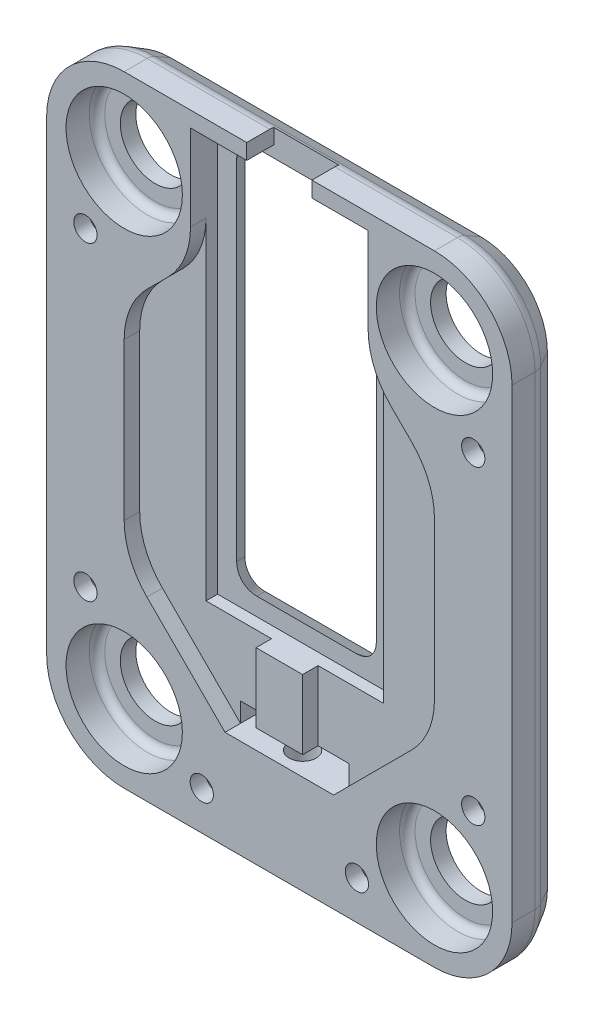
SolidWorks part; units mm, degrees
ref_plane "Front Plane" through (0, 0, 0) normal (0, 0, 1) x (1, 0, 0)
ref_plane "Top Plane" through (0, 0, 0) normal (0, 1, 0) x (1, 0, 0)
ref_plane "Right Plane" through (0, 0, 0) normal (1, 0, 0) x (0, 0, -1)
sketch "Sketch1" plane through (0, 0, 0) normal (0, 0, 1) x (1, 0, 0)
  line L1 (-11.25, 0) -> (11.25, 0) construction
  line L2 (-11.25, 0) -> (-11.25, -53) construction
  line L3 (-11.25, -53) -> (11.25, -53) construction
  line L4 (11.25, 0) -> (11.25, -53) construction
  line L5 (-4, 2) -> (4, 2) construction
  line L6 (-4, 2) -> (-4, 0) construction
  line L8 (4, 2) -> (4, 0) construction
  point P4 (0, 0)
  point P12 (0, 2)
  dimension "D1" = 22.5
  dimension "D2" = 53
  dimension "D3" = 8
  dimension "D4" = 2
sketch "Sketch2" plane through (0, 0, 0) normal (0, 0, 1) x (1, 0, 0)
  line L0 (-4, 2) -> (4, 2) construction
  line L1 (-20, 2) -> (20, 2)
  line L2 (-30, -8) -> (-30, -68)
  line L3 (-20, -78) -> (20, -78)
  line L4 (30, -8) -> (30, -68)
  arc A0 (-30, -68) -> (-20, -78) centre (-20, -68) ccw
  arc A1 (20, -78) -> (30, -68) centre (20, -68) ccw
  arc A2 (20, 2) -> (30, -8) centre (20, -8) cw
  arc A3 (-20, 2) -> (-30, -8) centre (-20, -8) ccw
  point P6 (0, 2)
  point P10 (-30, -78)
  point P15 (30, 2)
  point P18 (-30, 2)
  dimension "D3" = 10
  dimension "D1" = 60
  dimension "D2" = 80
extrude "Boss-Extrude1" add sketch "Sketch2" along normal blind 6
chamfer "Chamfer1" distance 2.5 angle 30 8 edges at (0, -78, 0) (27.0711, -75.0711, 0) (-27.0711, -75.0711, 0) (30, -38, 0) (-30, -38, 0) (27.0711, -0.9289, 0) (-27.0711, -0.9289, 0) (0, 2, 0)
fillet "Fillet1" radius 2 8 edges at (30, -38, 2.5) (27.0711, -75.0711, 2.5) (0, -78, 2.5) (-27.0711, -75.0711, 2.5) (-30, -38, 2.5) (-27.0711, -0.9289, 2.5) (0, 2, 2.5) (27.0711, -0.9289, 2.5)
sketch "Sketch10" plane through (0, 0, 6) normal (0, 0, 1) x (1, 0, 0)
  line L0 (-20, -8) -> (20, -8) construction
  line L1 (20, 2) -> (-20, 2) construction
  circle A0 centre (-20, -8) radius 4.5
  circle A1 centre (20, -8) radius 4.5
  circle A2 centre (20, -68) radius 4.5
  circle A3 centre (-20, -68) radius 4.5
  point P8 (0, -8)
  dimension "D1" = 9
  dimension "D2" = 40
  dimension "D3" = 60
  dimension "D4" = 10
extrude "Cut-Extrude1" cut sketch "Sketch10" against normal blind 6
sketch "Sketch11" plane through (0, 0, 6) normal (0, 0, 1) x (1, 0, 0)
  circle A0 centre (-20, -8) radius 7.5
  circle A1 centre (-20, -8) radius 4.5 construction
  circle A2 centre (20, -8) radius 7.5
  circle A3 centre (20, -68) radius 7.5
  circle A4 centre (-20, -68) radius 7.5
  circle A5 centre (-20, -68) radius 4.5 construction
  dimension "D1" = 15
extrude "Cut-Extrude2" cut sketch "Sketch11" against normal blind 4
sketch "Sketch12" plane through (0, 0, 6) normal (0, 0, 1) x (1, 0, 0)
  line L0 (-4.2, 2) -> (-4.2, 0)
  line L1 (-4.2, 0) -> (-11.45, 0)
  line L2 (-11.45, 0) -> (-11.45, -53.8)
  line L3 (-11.45, -53.8) -> (11.45, -53.8)
  line L4 (11.45, -53.8) -> (11.45, 0)
  line L5 (11.45, 0) -> (4.2, 0)
  line L6 (4.2, 0) -> (4.2, 2)
  line L7 (4.2, 2) -> (-4.2, 2)
  line L8 (-11.25, 0) -> (11.25, 0) construction
  line L9 (-4, 2) -> (-4, 0) construction
  line L10 (4, 2) -> (4, 0) construction
  line L11 (-11.25, 0) -> (-11.25, -53) construction
  line L12 (11.25, 0) -> (11.25, -53) construction
  line L13 (-11.25, -53) -> (11.25, -53) construction
  dimension "D1" = 0.2
  dimension "D2" = 0.2
  dimension "D3" = 0.2
  dimension "D4" = 0.2
  dimension "D5" = 0.8
  dimension "D6" = 2
extrude "Cut-Extrude3" cut sketch "Sketch12" against normal blind 3.5
sketch "Sketch13" plane through (0, 0, 2.5) normal (0, 0, 1) x (1, 0, 0)
  line L6 (-11.25, 0) -> (11.25, 0) construction
  line L7 (-9, -1.5) -> (9, -1.5)
  line L8 (-9, -1.5) -> (-9, -51.5)
  line L9 (-9, -51.5) -> (9, -51.5)
  line L10 (9, -1.5) -> (9, -51.5)
  point P6 (0, -1.5)
  dimension "D1" = 18
  dimension "D2" = 50
  dimension "D3" = 1.5
extrude "Cut-Extrude4" cut sketch "Sketch13" against normal through all draft 30
fillet "Fillet2" radius 3 4 edges at (-9.7217, -52.2217, 1.25) (9.7217, -52.2217, 1.25) (9.7217, -0.7783, 1.25) (-9.7217, -0.7783, 1.25)
hole_wizard "CBORE for M5 Hex Socket Head Cap Screw2" positions "Sketch22" profile "Sketch23" counterbore size "M5" standard "DIN" end condition through all
sketch "Sketch22" plane through (0, 0, 0) normal (0, 0, -1) x (-1, 0, 0)
  line L0 (4.2, 2) -> (20, 2) construction
  line L1 (20, -78) -> (-20, -78) construction
  line L2 (30, -8) -> (30, -68) construction
  line L3 (0, 16.14) -> (0, -89.9749) construction
  point P0 (-25, -18)
  point P2 (25, -18)
  point P4 (-10, -73)
  point P6 (10, -73)
  point P22 (25, -58)
  point P24 (-25, -58)
  dimension "D1" = 20
  dimension "D2" = 5
  dimension "D3" = 20
  dimension "D4" = 20
  dimension "D5" = 5
sketch "Sketch23" plane through (25, -18, 0) normal (1, 0, 0) x (0, 1, 0)
  line L0 (0, 0) -> (0, 6)
  line L1 (0, 6) -> (1.5, 6)
  line L3 (1.5, 6) -> (1.5, 4)
  line L4 (1.5, 4) -> (2, 4)
  line L5 (2, 4) -> (2, 0)
  line L7 (2, 0) -> (0, 0)
  line L11 (0, -6.35) -> (0, 107.95) construction
  dimension "Thru Hole Dia." = 3
  dimension "Thru Hole Depth" = 6
  dimension "C'Bore Dia." = 4
  dimension "C'Bore Depth" = 4
chamfer "Chamfer2" distance 2.5 angle 10 4 edges at (8, -73, 0) (-12, -73, 0) (-27, -18, 0) (23, -18, 0)
fillet "Fillet3" radius 1 4 edges at (-12.5, -8, 2) (-12.5, -68, 2) (27.5, -68, 2) (27.5, -8, 2)
sketch "Sketch24" plane through (0, 0, 6) normal (0, 0, 1) x (1, 0, 0)
  line L0 (-20, -78) -> (20, -78) construction
  line L1 (-7, -62.75) -> (7, -62.75)
  line L2 (-7, -62.75) -> (-7, -65.25)
  line L3 (-7, -65.25) -> (7, -65.25)
  line L4 (7, -62.75) -> (7, -65.25)
  point P6 (0, -65.25)
  dimension "D1" = 14
  dimension "D2" = 2.5
  dimension "D3" = 12.75
extrude "Cut-Extrude5" cut sketch "Sketch24" against normal through all
hole_wizard "M4 Tapped Hole1" positions "Sketch25" profile "Sketch26" tap size "M4" standard "DIN"
sketch "Sketch25" plane through (0, -78, 0) normal (0, -1, 0) x (-1, 0, 0)
  line L0 (20, -6) -> (-20, -6) construction
  point P0 (0, -3)
  dimension "D1" = 3
sketch "Sketch26" plane through (0, -78, 3) normal (1, 0, 0) x (0, 0, -1)
  line L0 (0, 0) -> (0, 12.75)
  line L1 (0, 12.75) -> (1.75, 12.75)
  line L2 (1.75, 12.75) -> (1.75, 0)
  line L5 (1.75, 0) -> (0, 0)
  line L11 (0, -6.35) -> (0, 107.95) construction
  dimension "Thread Major Dia." = 3.5
  dimension "Thru Tap Drill Depth" = 12.75
sketch "Sketch27" plane through (0, 0, 6) normal (0, 0, 1) x (1, 0, 0)
  line L0 (3, -10.75) -> (7, -10.75)
  line L1 (7, -10.75) -> (20, -23.75)
  line L2 (20, -23.75) -> (20, -52.25)
  line L3 (20, -52.25) -> (7, -65.25)
  line L4 (7, -65.25) -> (7, -64.2906)
  line L5 (7, -65.25) -> (7, -62.75) construction
  line L6 (7, -64.2906) -> (3, -64.2906)
  line L7 (3, -64.2906) -> (3, -10.75)
  line L9 (30, -68) -> (30, -8) construction
  line L10 (-20, -78) -> (20, -78) construction
  line L11 (20, 2) -> (4.2, 2) construction
  line L12 (0, 10.9936) -> (0, -34.5429) construction
  line L13 (-3, -64.2906) -> (-3, -10.75)
  line L14 (-7, -64.2906) -> (-3, -64.2906)
  line L15 (-7, -65.25) -> (-7, -64.2906)
  line L16 (-20, -52.25) -> (-7, -65.25)
  line L17 (-20, -23.75) -> (-20, -52.25)
  line L18 (-7, -10.75) -> (-20, -23.75)
  line L19 (-3, -10.75) -> (-7, -10.75)
  point P16 (12.1, 2)
  dimension "D1" = 135
  dimension "D2" = 135
  dimension "D3" = 10
  dimension "D4" = 4
  dimension "D5" = 12.75
  dimension "D7" = 12.75
extrude "Cut-Extrude6" cut sketch "Sketch27" against normal blind 2
fillet "Fillet4" radius 10 6 edges at (-11.45, -15.2, 5) (-20, -23.75, 5) (-20, -52.25, 5) (20, -52.25, 5) (20, -23.75, 5) (11.45, -15.2, 5)
